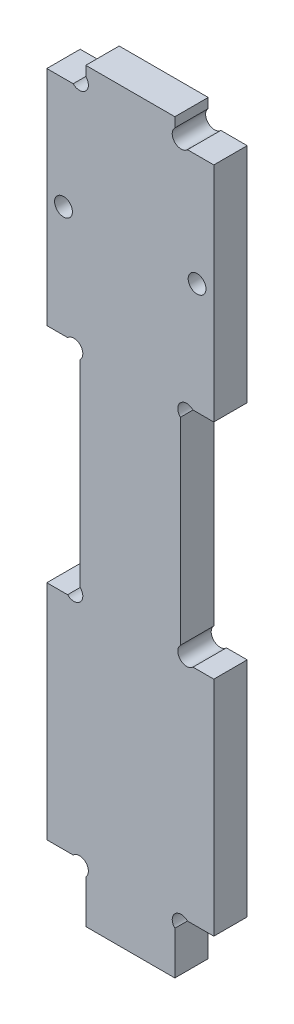
SolidWorks part; units mm, degrees
ref_plane "Plan de face" through (0, 0, 0) normal (0, 0, 1) x (1, 0, 0)
ref_plane "Plan de dessus" through (0, 0, 0) normal (0, 1, 0) x (1, 0, 0)
ref_plane "Plan de droite" through (0, 0, 0) normal (1, 0, 0) x (0, 0, -1)
sketch "Esquisse1" plane through (0, 0, 0) normal (0, 0, 1) x (1, 0, 0)
  line L0 (-5.6402, 0) -> (77.8383, 0) construction
  line L1 (0, -4.6127) -> (0, 153.108) construction
  line L2 (-5.6402, 134) -> (77.8383, 134) construction
  line L3 (30, -4.6127) -> (30, 153.108) construction
  line L4 (15, -4.6127) -> (15, 143.0755) construction
  line L5 (-5.6402, 10) -> (41.956, 10) construction
  line L6 (-5.6402, 130) -> (41.956, 130) construction
  line L7 (-5.6402, 70) -> (41.956, 70) construction
  line L8 (-5.6402, 50) -> (41.956, 50) construction
  line L9 (23, 143.0755) -> (23, -4.6127) construction
  line L10 (10.2189, 30) -> (41.956, 30) construction
  line L11 (24, -4.6127) -> (24, 143.0788) construction
  line L12 (27, 36.3609) -> (27, 16.7601) construction
  line L13 (24, 50) -> (33.3589, 59.3589) construction
  line L14 (25.2627, 10) -> (30, 10)
  line L15 (23, 10) -> (31.2888, 1.7112) construction
  line L16 (30, 50) -> (30, 10)
  line L17 (26.2627, 50) -> (30, 50)
  line L18 (25.2627, 130) -> (30, 130)
  line L19 (30, 90) -> (30, 130)
  line L20 (26.2627, 90) -> (30, 90)
  line L21 (3.7373, 90) -> (0, 90)
  line L22 (0, 90) -> (0, 130)
  line L23 (4.7373, 130) -> (0, 130)
  line L24 (3.7373, 50) -> (0, 50)
  line L25 (0, 50) -> (0, 10)
  line L26 (4.7373, 10) -> (0, 10)
  line L27 (23, 132.2627) -> (23, 134)
  line L28 (23, 7.7373) -> (23, 0)
  line L29 (24, 87.7373) -> (24, 52.2627)
  line L30 (7, 132.2627) -> (7, 134)
  line L31 (6, 87.7373) -> (6, 52.2627)
  line L32 (7, 7.7373) -> (7, 0)
  line L33 (7, 134) -> (23, 134)
  line L34 (7, 0) -> (23, 0)
  arc A1 (25.2627, 10) -> (23, 7.7373) centre (24.1314, 8.8686) ccw
  arc A2 (24, 52.2627) -> (26.2627, 50) centre (25.1314, 51.1314) ccw
  arc A3 (25.2627, 130) -> (23, 132.2627) centre (24.1314, 131.1314) cw
  circle A4 centre (27, 110) radius 1.6
  arc A5 (24, 87.7373) -> (26.2627, 90) centre (25.1314, 88.8686) cw
  arc A6 (6, 87.7373) -> (3.7373, 90) centre (4.8686, 88.8686) ccw
  circle A7 centre (3, 110) radius 1.6
  arc A8 (4.7373, 130) -> (7, 132.2627) centre (5.8686, 131.1314) ccw
  arc A9 (6, 52.2627) -> (3.7373, 50) centre (4.8686, 51.1314) cw
  arc A10 (4.7373, 10) -> (7, 7.7373) centre (5.8686, 8.8686) cw
  dimension "D13" = 45
  dimension "D1" = 134
  dimension "D2" = 30
  dimension "D3" = 4
  dimension "D4" = 60
  dimension "D5" = 20
  dimension "D6" = 10
  dimension "D7" = 15
  dimension "D8" = 8
  dimension "D9" = 20
  dimension "D10" = 6
  dimension "D11" = 3
  dimension "D12" = 45
extrude "Extrusion1" add sketch "Esquisse1" along normal blind 6
